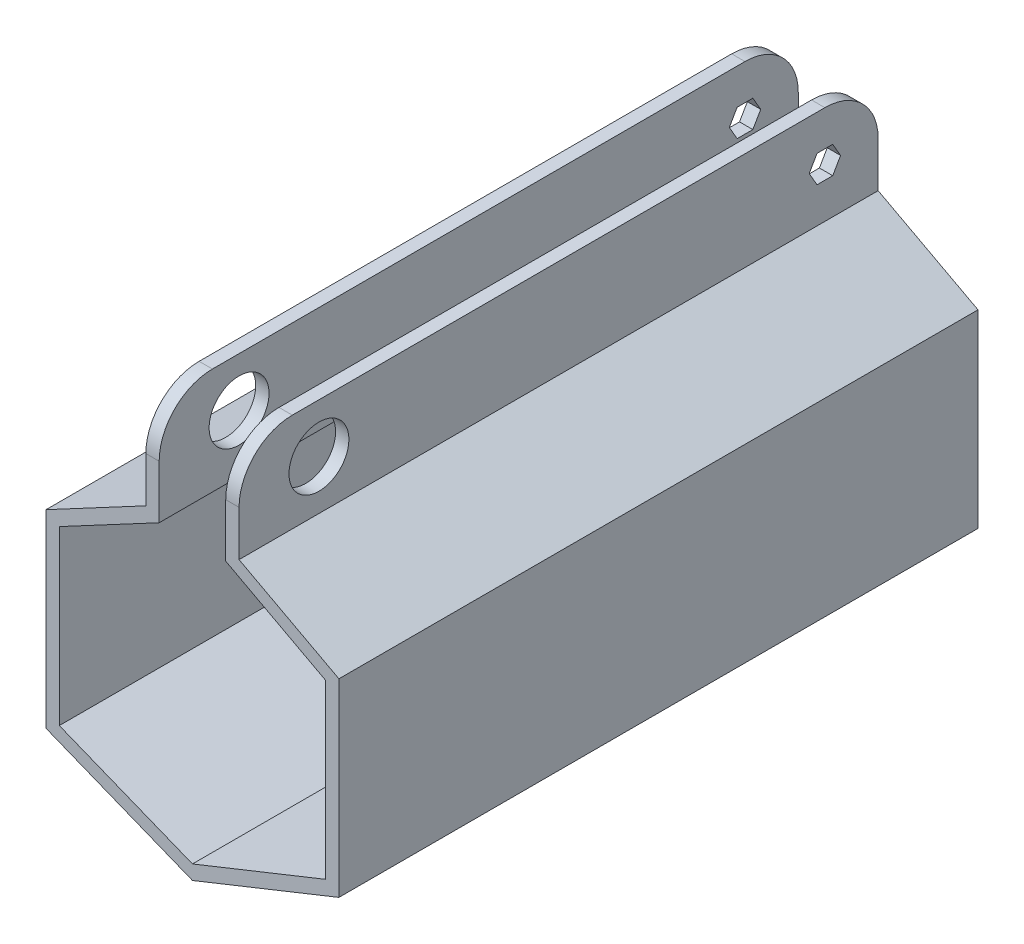
SolidWorks part; units mm, degrees
ref_plane "Front Plane" through (0, 0, 0) normal (0, 0, 1) x (1, 0, 0)
ref_plane "Top Plane" through (0, 0, 0) normal (0, 1, 0) x (1, 0, 0)
ref_plane "Right Plane" through (0, 0, 0) normal (1, 0, 0) x (0, 0, -1)
sketch "Sketch1" plane through (0, 0, 0) normal (0, 0, 1) x (1, 0, 0)
  line L0 (0, 0) -> (-63.5, 25.4)
  line L1 (-63.5, 25.4) -> (-63.5, 107.5899)
  line L2 (-63.5, 107.5899) -> (-15.875, 132.9899)
  line L3 (0, 0) -> (63.5, 25.4)
  line L4 (63.5, 25.4) -> (63.5, 107.5899)
  line L5 (63.5, 107.5899) -> (15.875, 132.9899)
  line L6 (0, 0) -> (0, -50000) construction
  line L7 (-12.7, 207.6024) -> (12.7, 207.6024) construction
  line L8 (-12.7, 207.6024) -> (-12.7, 106.0024) construction
  line L9 (-12.7, 106.0024) -> (12.7, 106.0024) construction
  line L10 (12.7, 207.6024) -> (12.7, 106.0024) construction
  line L11 (-15.875, 132.9899) -> (-15.875, 183.7899)
  line L12 (15.875, 132.9899) -> (15.875, 183.7899)
  line L13 (22.225, 136.7999) -> (22.225, 183.7899)
  line L14 (-25.4, 171.0899) -> (25.4, 171.0899) construction
  line L15 (-25.4, 171.0899) -> (-25.4, 142.5149) construction
  line L16 (-25.4, 142.5149) -> (25.4, 142.5149) construction
  line L17 (25.4, 171.0899) -> (25.4, 142.5149) construction
  line L18 (69.85, 111.3999) -> (22.225, 136.7999)
  line L19 (69.85, 21.1008) -> (69.85, 111.3999)
  line L20 (0, -6.8392) -> (69.85, 21.1008)
  line L21 (0, -6.8392) -> (-69.85, 21.1008)
  line L22 (-69.85, 21.1008) -> (-69.85, 111.3999)
  line L23 (-69.85, 111.3999) -> (-22.225, 136.7999)
  line L24 (-22.225, 136.7999) -> (-22.225, 183.7899)
  line L25 (-22.225, 183.7899) -> (-15.875, 183.7899)
  line L26 (15.875, 183.7899) -> (22.225, 183.7899)
  circle A0 centre (0, 61.5524) radius 57.15 construction
  point P2 (-12.7, 156.8024)
  point P18 (25.4, 156.8024)
  point P19 (0, 171.0899)
  point P25 (0, 106.0024)
  dimension "D1" = 114.3
  dimension "D2" = 31.75
  dimension "D3" = 127
  dimension "D4" = 101.6
  dimension "D5" = 25.4
  dimension "D6" = 25.4
  dimension "D7" = 12.7
  dimension "D8" = 25.4
  dimension "D9" = 50.8
  dimension "D10" = 28.575
  dimension "D11" = 50.8
  dimension "D12" = 12.7
  dimension "D13" = 6.35
extrude "Boss-Extrude1" add sketch "Sketch1" along normal blind 304.8
sketch "Sketch2" plane through (22.225, 0, 0) normal (1, 0, 0) x (0, 0, -1)
  line L0 (0, 136.7999) -> (0, 183.7899) construction
  line L2 (-17.921, 160.2949) -> (-21.6605, 166.7719)
  line L3 (-21.6605, 166.7719) -> (-29.1395, 166.7719)
  line L4 (-29.1395, 166.7719) -> (-32.879, 160.2949)
  line L5 (-32.879, 160.2949) -> (-29.1395, 153.8179)
  line L6 (-29.1395, 153.8179) -> (-21.6605, 153.8179)
  line L7 (-21.6605, 153.8179) -> (-17.921, 160.2949)
  circle A1 centre (-266.7, 160.2949) radius 14.2875
  circle A2 centre (-266.7, 160.2949) radius 50.8 construction
  circle A5 centre (-25.4, 160.2949) radius 6.477 construction
  point P4 (0, 160.2949)
  point P10 (-25.4, 166.7719)
  dimension "D1" = 12.954
  dimension "D3" = 101.6
  dimension "D4" = 28.575
  dimension "D2" = 266.7
  dimension "D5" = 25.4
extrude "Cut-Extrude1" cut sketch "Sketch2" against normal blind 304.8
fillet "Fillet1" radius 25.4 2 edges at (-19.05, 183.7899, 0) (19.05, 183.7899, 0)
fillet "Fillet2" radius 25.4 2 edges at (19.05, 183.7899, 304.8) (-19.05, 183.7899, 304.8)
